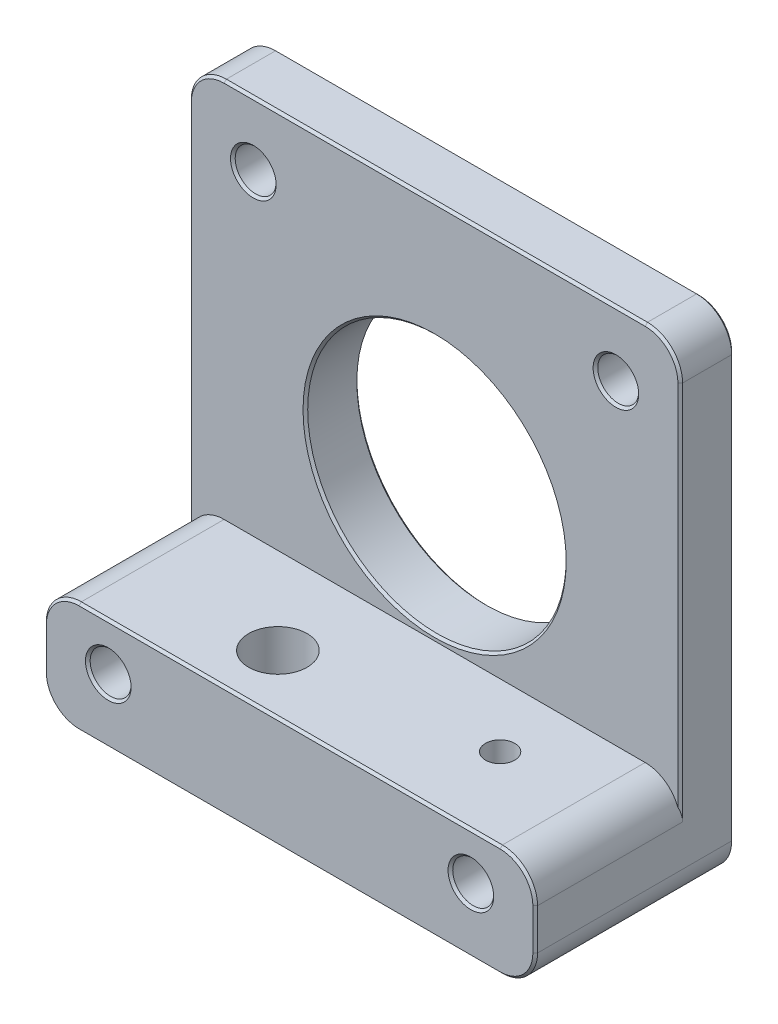
SolidWorks part; units mm, degrees
ref_plane "Спереди" through (0, 0, 0) normal (0, 0, 1) x (1, 0, 0)
ref_plane "Сверху" through (0, 0, 0) normal (0, 1, 0) x (1, 0, 0)
ref_plane "Справа" through (0, 0, 0) normal (1, 0, 0) x (0, 0, -1)
sketch "Эскиз1" plane through (0, 0, 0) normal (0, 0, 1) x (1, 0, 0)
  line L1 (0, 0) -> (42, 0)
  line L2 (0, 0) -> (0, 42)
  line L3 (0, 42) -> (42, 42)
  line L4 (42, 0) -> (42, 42)
  dimension "D1" = 42
  dimension "D2" = 42
extrude "Бобышка-Вытянуть1" add sketch "Эскиз1" along normal blind 17
sketch "Эскиз2" plane through (0, 0, 17) normal (0, 0, 1) x (1, 0, 0)
  line L0 (42, 0) -> (42, 42) construction
  line L1 (0, 42) -> (42, 42)
  line L2 (0, 42) -> (0, 9.5)
  line L3 (0, 9.5) -> (42, 9.5)
  line L4 (42, 42) -> (42, 9.5)
  line L5 (0, 0) -> (42, 0) construction
  dimension "D1" = 9.5
extrude "Вырез-Вытянуть1" cut sketch "Эскиз2" against normal blind 12.4
sketch "Эскиз3" plane through (0, 0, 0) normal (0, 0, -1) x (-1, 0, 0)
  circle A0 centre (-21, 21) radius 11.05
extrude "Вырез-Вытянуть2" cut sketch "Эскиз3" against normal blind 12.4
sketch "Эскиз4" plane through (0, 9.5, 0) normal (0, 1, 0) x (1, 0, 0)
  line L0 (0, -17) -> (42, -17) construction
  line L1 (0, -4.6) -> (0, -17) construction
  circle A0 centre (15, -12) radius 2.5
  dimension "D1" = 5
  dimension "D2" = 15
extrude "Вырез-Вытянуть3" cut sketch "Эскиз4" against normal blind 12.4
sketch "Эскиз5" plane through (0, 9.5, 0) normal (0, 1, 0) x (1, 0, 0)
  line L0 (0, -17) -> (42, -17) construction
  line L1 (42, -4.6) -> (42, -17) construction
  circle A0 centre (32, -10) radius 1.25
  dimension "D1" = 7
  dimension "D2" = 10
extrude "Вырез-Вытянуть4" cut sketch "Эскиз5" against normal blind 12.4
fillet "Скругление1" radius 3 6 edges at (42, 42, 2.3) (0, 42, 2.3) (42, 0, 8.5) (42, 9.5, 10.8) (0, 0, 8.5) (0, 9.5, 10.8)
chamfer "Фаска1" distance 0.2 angle 45 9 edges at (0.8787, 41.1213, 0) (0, 21, 0) (0.8787, 0.8787, 0) (21, 0, 0) (41.1213, 0.8787, 0) (42, 21, 0) (41.1213, 41.1213, 0) (21, 42, 0) (9.95, 21, 0)
chamfer "Фаска2" distance 0.2 angle 45 13 edges at (0.8787, 0.8787, 17) (0, 4.75, 17) (0.8787, 8.6213, 17) (21, 9.5, 17) (41.1213, 8.6213, 17) (42, 4.75, 17) (41.1213, 0.8787, 17) (21, 0, 17) (42, 22.75, 4.6) (41.1213, 41.1213, 4.6) (21, 42, 4.6) (0.8787, 41.1213, 4.6) (0, 22.75, 4.6)
chamfer "Фаска3" distance 0.2 angle 45 1 edges at (32.05, 21, 4.6)
sketch "Эскиз6" plane through (0, 0, 0) normal (0, 0, -1) x (-1, 0, 0)
  circle A0 centre (-5.5, 36.5) radius 1.75
  circle A1 centre (-36.5, 36.5) radius 1.75
  circle A2 centre (-5.5, 5.5) radius 1.75
  circle A3 centre (-36.5, 5.5) radius 1.75
extrude "Вырез-Вытянуть5" cut sketch "Эскиз6" against normal blind 26
chamfer "Фаска4" distance 0.2 angle 45 8 edges at (3.75, 36.5, 0) (34.75, 36.5, 0) (34.75, 5.5, 0) (3.75, 5.5, 0) (3.75, 5.5, 17) (34.75, 5.5, 17) (38.25, 36.5, 4.6) (7.25, 36.5, 4.6)
